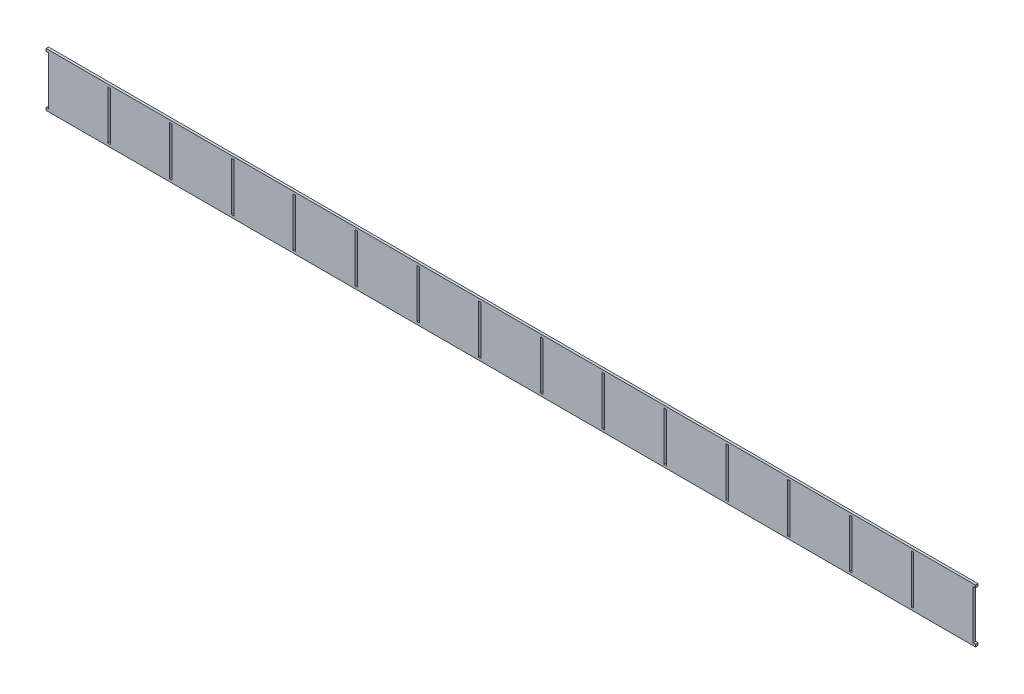
SolidWorks part; units mm, degrees
material "Cedar"
ref_plane "Front Plane" through (0, 0, 0) normal (0, 0, 1) x (1, 0, 0)
ref_plane "Top Plane" through (0, 0, 0) normal (0, 1, 0) x (1, 0, 0)
ref_plane "Right Plane" through (0, 0, 0) normal (1, 0, 0) x (0, 0, -1)
sketch "Sketch2" plane through (0, 0, 0) normal (0, 0, 1) x (1, 0, 0)
  line L0 (-778.4916, 45.21) -> (-778.4916, 41.21)
  line L1 (-778.4916, 41.21) -> (-774.4916, 41.21)
  line L2 (-774.4916, 41.21) -> (-774.4916, 1.805)
  line L3 (-774.4916, 1.805) -> (-750.4916, 1.805)
  line L4 (-756.4916, 9.805) -> (-732.4916, 9.805)
  line L5 (-750.4916, 1.805) -> (-756.4916, 9.805)
  line L6 (-738.4916, 1.805) -> (-714.4916, 1.805)
  line L7 (-738.4916, 1.805) -> (-732.4916, 9.805)
  line L8 (-578.4916, 41.21) -> (-574.4916, 41.21)
  line L9 (-714.4916, 1.805) -> (-720.4916, 9.805)
  line L10 (-720.4916, 9.805) -> (-696.4916, 9.805)
  line L11 (-702.4916, 1.805) -> (-696.4916, 9.805)
  line L12 (-702.4916, 1.805) -> (-678.4916, 1.805)
  line L13 (-778.4916, 45.21) -> (725.5084, 45.21)
  line L14 (-678.4916, 1.805) -> (-678.4916, 41.21)
  line L15 (-678.4916, 41.21) -> (-674.4916, 41.21)
  line L16 (-674.4916, 41.21) -> (-674.4916, 1.805)
  line L17 (-674.4916, 1.805) -> (-650.4916, 1.805)
  line L18 (-656.4916, 9.805) -> (-632.4916, 9.805)
  line L19 (-650.4916, 1.805) -> (-656.4916, 9.805)
  line L20 (-638.4916, 1.805) -> (-614.4916, 1.805)
  line L21 (-638.4916, 1.805) -> (-632.4916, 9.805)
  line L22 (-614.4916, 1.805) -> (-620.4916, 9.805)
  line L23 (-620.4916, 9.805) -> (-596.4916, 9.805)
  line L24 (-602.4916, 1.805) -> (-596.4916, 9.805)
  line L25 (-602.4916, 1.805) -> (-578.4916, 1.805)
  line L26 (-578.4916, 1.805) -> (-578.4916, 41.21)
  line L27 (-774.4916, 1.805) -> (855.8499, 1.805) construction
  line L28 (-574.4916, 41.21) -> (-574.4916, 1.805)
  line L29 (-574.4916, 1.805) -> (-550.4916, 1.805)
  line L30 (-556.4916, 9.805) -> (-532.4916, 9.805)
  line L31 (-550.4916, 1.805) -> (-556.4916, 9.805)
  line L32 (-538.4916, 1.805) -> (-514.4916, 1.805)
  line L33 (-538.4916, 1.805) -> (-532.4916, 9.805)
  line L34 (-514.4916, 1.805) -> (-520.4916, 9.805)
  line L35 (-520.4916, 9.805) -> (-496.4916, 9.805)
  line L36 (-502.4916, 1.805) -> (-496.4916, 9.805)
  line L37 (-502.4916, 1.805) -> (-478.4916, 1.805)
  line L38 (-478.4916, 1.805) -> (-478.4916, 41.21)
  line L39 (-478.4916, 41.21) -> (-474.4916, 41.21)
  line L40 (-474.4916, 41.21) -> (-474.4916, 1.805)
  line L41 (-474.4916, 1.805) -> (-450.4916, 1.805)
  line L42 (-456.4916, 9.805) -> (-432.4916, 9.805)
  line L43 (-450.4916, 1.805) -> (-456.4916, 9.805)
  line L44 (-438.4916, 1.805) -> (-414.4916, 1.805)
  line L45 (-438.4916, 1.805) -> (-432.4916, 9.805)
  line L46 (-414.4916, 1.805) -> (-420.4916, 9.805)
  line L47 (-420.4916, 9.805) -> (-396.4916, 9.805)
  line L48 (-402.4916, 1.805) -> (-396.4916, 9.805)
  line L49 (-402.4916, 1.805) -> (-378.4916, 1.805)
  line L50 (-378.4916, 1.805) -> (-378.4916, 41.21)
  line L51 (-378.4916, 41.21) -> (-374.4916, 41.21)
  line L52 (-374.4916, 41.21) -> (-374.4916, 1.805)
  line L53 (-374.4916, 1.805) -> (-350.4916, 1.805)
  line L54 (-356.4916, 9.805) -> (-332.4916, 9.805)
  line L55 (-350.4916, 1.805) -> (-356.4916, 9.805)
  line L56 (-338.4916, 1.805) -> (-314.4916, 1.805)
  line L57 (-338.4916, 1.805) -> (-332.4916, 9.805)
  line L58 (-314.4916, 1.805) -> (-320.4916, 9.805)
  line L59 (-320.4916, 9.805) -> (-296.4916, 9.805)
  line L60 (-302.4916, 1.805) -> (-296.4916, 9.805)
  line L61 (-302.4916, 1.805) -> (-278.4916, 1.805)
  line L62 (-278.4916, 1.805) -> (-278.4916, 41.21)
  line L63 (-278.4916, 41.21) -> (-274.4916, 41.21)
  line L64 (-274.4916, 41.21) -> (-274.4916, 1.805)
  line L65 (-274.4916, 1.805) -> (-250.4916, 1.805)
  line L66 (-256.4916, 9.805) -> (-232.4916, 9.805)
  line L67 (-250.4916, 1.805) -> (-256.4916, 9.805)
  line L68 (-238.4916, 1.805) -> (-214.4916, 1.805)
  line L69 (-238.4916, 1.805) -> (-232.4916, 9.805)
  line L70 (-214.4916, 1.805) -> (-220.4916, 9.805)
  line L71 (-220.4916, 9.805) -> (-196.4916, 9.805)
  line L72 (-202.4916, 1.805) -> (-196.4916, 9.805)
  line L73 (-202.4916, 1.805) -> (-178.4916, 1.805)
  line L74 (-178.4916, 1.805) -> (-178.4916, 41.21)
  line L75 (-178.4916, 41.21) -> (-174.4916, 41.21)
  line L76 (-174.4916, 41.21) -> (-174.4916, 1.805)
  line L77 (-174.4916, 1.805) -> (-150.4916, 1.805)
  line L78 (-156.4916, 9.805) -> (-132.4916, 9.805)
  line L79 (-150.4916, 1.805) -> (-156.4916, 9.805)
  line L80 (-138.4916, 1.805) -> (-114.4916, 1.805)
  line L81 (-138.4916, 1.805) -> (-132.4916, 9.805)
  line L82 (-114.4916, 1.805) -> (-120.4916, 9.805)
  line L83 (-120.4916, 9.805) -> (-96.4916, 9.805)
  line L84 (-102.4916, 1.805) -> (-96.4916, 9.805)
  line L85 (-102.4916, 1.805) -> (-78.4916, 1.805)
  line L86 (-78.4916, 1.805) -> (-78.4916, 41.21)
  line L87 (-78.4916, 41.21) -> (-74.4916, 41.21)
  line L88 (-74.4916, 41.21) -> (-74.4916, 1.805)
  line L89 (-74.4916, 1.805) -> (-50.4916, 1.805)
  line L90 (-56.4916, 9.805) -> (-32.4916, 9.805)
  line L91 (-50.4916, 1.805) -> (-56.4916, 9.805)
  line L92 (-38.4916, 1.805) -> (-14.4916, 1.805)
  line L93 (-38.4916, 1.805) -> (-32.4916, 9.805)
  line L94 (-14.4916, 1.805) -> (-20.4916, 9.805)
  line L95 (-20.4916, 9.805) -> (3.5084, 9.805)
  line L96 (-2.4916, 1.805) -> (3.5084, 9.805)
  line L97 (-2.4916, 1.805) -> (21.5084, 1.805)
  line L98 (21.5084, 1.805) -> (21.5084, 41.21)
  line L99 (21.5084, 41.21) -> (25.5084, 41.21)
  line L100 (25.5084, 41.21) -> (25.5084, 1.805)
  line L101 (25.5084, 1.805) -> (49.5084, 1.805)
  line L102 (43.5084, 9.805) -> (67.5084, 9.805)
  line L103 (49.5084, 1.805) -> (43.5084, 9.805)
  line L104 (61.5084, 1.805) -> (85.5084, 1.805)
  line L105 (61.5084, 1.805) -> (67.5084, 9.805)
  line L106 (85.5084, 1.805) -> (79.5084, 9.805)
  line L107 (79.5084, 9.805) -> (103.5084, 9.805)
  line L108 (97.5084, 1.805) -> (103.5084, 9.805)
  line L109 (97.5084, 1.805) -> (121.5084, 1.805)
  line L110 (121.5084, 1.805) -> (121.5084, 41.21)
  line L111 (121.5084, 41.21) -> (125.5084, 41.21)
  line L112 (125.5084, 41.21) -> (125.5084, 1.805)
  line L113 (125.5084, 1.805) -> (149.5084, 1.805)
  line L114 (143.5084, 9.805) -> (167.5084, 9.805)
  line L115 (149.5084, 1.805) -> (143.5084, 9.805)
  line L116 (161.5084, 1.805) -> (185.5084, 1.805)
  line L117 (161.5084, 1.805) -> (167.5084, 9.805)
  line L118 (185.5084, 1.805) -> (179.5084, 9.805)
  line L119 (179.5084, 9.805) -> (203.5084, 9.805)
  line L120 (197.5084, 1.805) -> (203.5084, 9.805)
  line L121 (197.5084, 1.805) -> (221.5084, 1.805)
  line L122 (221.5084, 1.805) -> (221.5084, 41.21)
  line L123 (221.5084, 41.21) -> (225.5084, 41.21)
  line L124 (225.5084, 41.21) -> (225.5084, 1.805)
  line L125 (225.5084, 1.805) -> (249.5084, 1.805)
  line L126 (243.5084, 9.805) -> (267.5084, 9.805)
  line L127 (249.5084, 1.805) -> (243.5084, 9.805)
  line L128 (261.5084, 1.805) -> (285.5084, 1.805)
  line L129 (261.5084, 1.805) -> (267.5084, 9.805)
  line L130 (285.5084, 1.805) -> (279.5084, 9.805)
  line L131 (279.5084, 9.805) -> (303.5084, 9.805)
  line L132 (297.5084, 1.805) -> (303.5084, 9.805)
  line L133 (297.5084, 1.805) -> (321.5084, 1.805)
  line L134 (321.5084, 1.805) -> (321.5084, 41.21)
  line L135 (321.5084, 41.21) -> (325.5084, 41.21)
  line L136 (325.5084, 41.21) -> (325.5084, 1.805)
  line L137 (325.5084, 1.805) -> (349.5084, 1.805)
  line L138 (343.5084, 9.805) -> (367.5084, 9.805)
  line L139 (349.5084, 1.805) -> (343.5084, 9.805)
  line L140 (361.5084, 1.805) -> (385.5084, 1.805)
  line L141 (361.5084, 1.805) -> (367.5084, 9.805)
  line L142 (385.5084, 1.805) -> (379.5084, 9.805)
  line L143 (379.5084, 9.805) -> (403.5084, 9.805)
  line L144 (397.5084, 1.805) -> (403.5084, 9.805)
  line L145 (397.5084, 1.805) -> (421.5084, 1.805)
  line L146 (421.5084, 1.805) -> (421.5084, 41.21)
  line L147 (421.5084, 41.21) -> (425.5084, 41.21)
  line L148 (425.5084, 41.21) -> (425.5084, 1.805)
  line L149 (425.5084, 1.805) -> (449.5084, 1.805)
  line L150 (443.5084, 9.805) -> (467.5084, 9.805)
  line L151 (449.5084, 1.805) -> (443.5084, 9.805)
  line L152 (461.5084, 1.805) -> (485.5084, 1.805)
  line L153 (461.5084, 1.805) -> (467.5084, 9.805)
  line L154 (485.5084, 1.805) -> (479.5084, 9.805)
  line L155 (479.5084, 9.805) -> (503.5084, 9.805)
  line L156 (497.5084, 1.805) -> (503.5084, 9.805)
  line L157 (497.5084, 1.805) -> (521.5084, 1.805)
  line L158 (521.5084, 1.805) -> (521.5084, 41.21)
  line L159 (521.5084, 41.21) -> (525.5084, 41.21)
  line L160 (525.5084, 41.21) -> (525.5084, 1.805)
  line L161 (525.5084, 1.805) -> (549.5084, 1.805)
  line L162 (543.5084, 9.805) -> (567.5084, 9.805)
  line L163 (549.5084, 1.805) -> (543.5084, 9.805)
  line L164 (561.5084, 1.805) -> (585.5084, 1.805)
  line L165 (561.5084, 1.805) -> (567.5084, 9.805)
  line L166 (585.5084, 1.805) -> (579.5084, 9.805)
  line L167 (579.5084, 9.805) -> (603.5084, 9.805)
  line L168 (597.5084, 1.805) -> (603.5084, 9.805)
  line L169 (597.5084, 1.805) -> (621.5084, 1.805)
  line L170 (621.5084, 1.805) -> (621.5084, 41.21)
  line L171 (621.5084, 41.21) -> (625.5084, 41.21)
  line L172 (625.5084, 41.21) -> (625.5084, 1.805)
  line L173 (625.5084, 1.805) -> (649.5084, 1.805)
  line L174 (643.5084, 9.805) -> (667.5084, 9.805)
  line L175 (649.5084, 1.805) -> (643.5084, 9.805)
  line L176 (661.5084, 1.805) -> (685.5084, 1.805)
  line L177 (661.5084, 1.805) -> (667.5084, 9.805)
  line L178 (685.5084, 1.805) -> (679.5084, 9.805)
  line L179 (679.5084, 9.805) -> (703.5084, 9.805)
  line L180 (697.5084, 1.805) -> (703.5084, 9.805)
  line L181 (697.5084, 1.805) -> (721.5084, 1.805)
  line L182 (721.5084, 1.805) -> (721.5084, 41.21)
  line L183 (725.5084, 45.21) -> (725.5084, 41.21)
  line L184 (725.5084, 41.21) -> (721.5084, 41.21)
  dimension "D2" = 4
  dimension "D3" = 4
  dimension "D4" = 1504
  dimension "D5" = 24
  dimension "D6" = 24
  dimension "D7" = 6
  dimension "D8" = 8
  dimension "D9" = 24
  dimension "D10" = 6
  dimension "D11" = 15
extrude "Boss-Extrude1" add sketch "Sketch2" along normal blind 4
sketch "Sketch3" plane through (0, 0, 4) normal (0, 0, 1) x (1, 0, 0)
  line L0 (-774.4916, 1.805) -> (-774.4916, -37.605)
  line L1 (-774.4916, -37.605) -> (-778.4916, -37.605)
  line L2 (-778.4916, -37.605) -> (-778.4916, -41.605)
  line L3 (-778.4916, -41.605) -> (725.5084, -41.605)
  line L4 (-674.4916, 1.805) -> (-674.4916, -37.605)
  line L5 (-774.4916, 1.805) -> (-750.4916, 1.805)
  line L6 (-750.4916, 1.805) -> (-756.4916, 9.805)
  line L7 (-756.4916, 9.805) -> (-732.4916, 9.805)
  line L8 (-732.4916, 9.805) -> (-738.4916, 1.805)
  line L9 (-738.4916, 1.805) -> (-714.4916, 1.805)
  line L10 (-714.4916, 1.805) -> (-720.4916, 9.805)
  line L11 (-720.4916, 9.805) -> (-696.4916, 9.805)
  line L12 (-696.4916, 9.805) -> (-702.4916, 1.805)
  line L13 (-702.4916, 1.805) -> (-678.4916, 1.805)
  line L14 (-678.4916, 1.805) -> (-678.4916, -37.605)
  line L15 (-674.4916, -37.605) -> (-678.4916, -37.605)
  line L16 (-674.4916, 1.805) -> (-650.4916, 1.805)
  line L17 (-650.4916, 1.805) -> (-656.4916, 9.805)
  line L18 (-656.4916, 9.805) -> (-632.4916, 9.805)
  line L19 (-632.4916, 9.805) -> (-638.4916, 1.805)
  line L20 (-638.4916, 1.805) -> (-614.4916, 1.805)
  line L21 (-614.4916, 1.805) -> (-620.4916, 9.805)
  line L22 (-620.4916, 9.805) -> (-596.4916, 9.805)
  line L23 (-596.4916, 9.805) -> (-602.4916, 1.805)
  line L24 (-602.4916, 1.805) -> (-578.4916, 1.805)
  line L25 (-578.4916, 1.805) -> (-578.4916, -37.605)
  line L26 (-574.4916, 1.805) -> (-574.4916, -37.605)
  line L27 (-574.4916, -37.605) -> (-578.4916, -37.605)
  line L28 (-574.4916, 1.805) -> (-550.4916, 1.805)
  line L29 (-550.4916, 1.805) -> (-556.4916, 9.805)
  line L30 (-556.4916, 9.805) -> (-532.4916, 9.805)
  line L31 (-532.4916, 9.805) -> (-538.4916, 1.805)
  line L32 (-538.4916, 1.805) -> (-514.4916, 1.805)
  line L33 (-514.4916, 1.805) -> (-520.4916, 9.805)
  line L34 (-520.4916, 9.805) -> (-496.4916, 9.805)
  line L35 (-496.4916, 9.805) -> (-502.4916, 1.805)
  line L36 (-502.4916, 1.805) -> (-478.4916, 1.805)
  line L37 (-478.4916, 1.805) -> (-478.4916, -37.605)
  line L38 (-474.4916, 1.805) -> (-474.4916, -37.605)
  line L39 (-474.4916, -37.605) -> (-478.4916, -37.605)
  line L40 (-474.4916, 1.805) -> (-450.4916, 1.805)
  line L41 (-450.4916, 1.805) -> (-456.4916, 9.805)
  line L42 (-456.4916, 9.805) -> (-432.4916, 9.805)
  line L43 (-432.4916, 9.805) -> (-438.4916, 1.805)
  line L44 (-438.4916, 1.805) -> (-414.4916, 1.805)
  line L45 (-414.4916, 1.805) -> (-420.4916, 9.805)
  line L46 (-420.4916, 9.805) -> (-396.4916, 9.805)
  line L47 (-396.4916, 9.805) -> (-402.4916, 1.805)
  line L48 (-402.4916, 1.805) -> (-378.4916, 1.805)
  line L49 (-378.4916, 1.805) -> (-378.4916, -37.605)
  line L50 (-374.4916, 1.805) -> (-374.4916, -37.605)
  line L51 (-374.4916, -37.605) -> (-378.4916, -37.605)
  line L52 (-374.4916, 1.805) -> (-350.4916, 1.805)
  line L53 (-350.4916, 1.805) -> (-356.4916, 9.805)
  line L54 (-356.4916, 9.805) -> (-332.4916, 9.805)
  line L55 (-332.4916, 9.805) -> (-338.4916, 1.805)
  line L56 (-338.4916, 1.805) -> (-314.4916, 1.805)
  line L57 (-314.4916, 1.805) -> (-320.4916, 9.805)
  line L58 (-320.4916, 9.805) -> (-296.4916, 9.805)
  line L59 (-296.4916, 9.805) -> (-302.4916, 1.805)
  line L60 (-302.4916, 1.805) -> (-278.4916, 1.805)
  line L61 (-278.4916, 1.805) -> (-278.4916, -37.605)
  line L62 (-274.4916, 1.805) -> (-274.4916, -37.605)
  line L63 (-274.4916, -37.605) -> (-278.4916, -37.605)
  line L64 (-274.4916, 1.805) -> (-250.4916, 1.805)
  line L65 (-250.4916, 1.805) -> (-256.4916, 9.805)
  line L66 (-256.4916, 9.805) -> (-232.4916, 9.805)
  line L67 (-232.4916, 9.805) -> (-238.4916, 1.805)
  line L68 (-238.4916, 1.805) -> (-214.4916, 1.805)
  line L69 (-214.4916, 1.805) -> (-220.4916, 9.805)
  line L70 (-220.4916, 9.805) -> (-196.4916, 9.805)
  line L71 (-196.4916, 9.805) -> (-202.4916, 1.805)
  line L72 (-202.4916, 1.805) -> (-178.4916, 1.805)
  line L73 (-178.4916, 1.805) -> (-178.4916, -37.605)
  line L74 (-174.4916, 1.805) -> (-174.4916, -37.605)
  line L75 (-174.4916, -37.605) -> (-178.4916, -37.605)
  line L76 (-174.4916, 1.805) -> (-150.4916, 1.805)
  line L77 (-150.4916, 1.805) -> (-156.4916, 9.805)
  line L78 (-156.4916, 9.805) -> (-132.4916, 9.805)
  line L79 (-132.4916, 9.805) -> (-138.4916, 1.805)
  line L80 (-138.4916, 1.805) -> (-114.4916, 1.805)
  line L81 (-114.4916, 1.805) -> (-120.4916, 9.805)
  line L82 (-120.4916, 9.805) -> (-96.4916, 9.805)
  line L83 (-96.4916, 9.805) -> (-102.4916, 1.805)
  line L84 (-102.4916, 1.805) -> (-78.4916, 1.805)
  line L85 (-78.4916, 1.805) -> (-78.4916, -37.605)
  line L86 (-74.4916, 1.805) -> (-74.4916, -37.605)
  line L87 (-74.4916, -37.605) -> (-78.4916, -37.605)
  line L88 (-74.4916, 1.805) -> (-50.4916, 1.805)
  line L89 (-50.4916, 1.805) -> (-56.4916, 9.805)
  line L90 (-56.4916, 9.805) -> (-32.4916, 9.805)
  line L91 (-32.4916, 9.805) -> (-38.4916, 1.805)
  line L92 (-38.4916, 1.805) -> (-14.4916, 1.805)
  line L93 (-14.4916, 1.805) -> (-20.4916, 9.805)
  line L94 (-20.4916, 9.805) -> (3.5084, 9.805)
  line L95 (3.5084, 9.805) -> (-2.4916, 1.805)
  line L96 (-2.4916, 1.805) -> (21.5084, 1.805)
  line L97 (21.5084, 1.805) -> (21.5084, -37.605)
  line L98 (25.5084, 1.805) -> (25.5084, -37.605)
  line L99 (25.5084, -37.605) -> (21.5084, -37.605)
  line L100 (25.5084, 1.805) -> (49.5084, 1.805)
  line L101 (49.5084, 1.805) -> (43.5084, 9.805)
  line L102 (43.5084, 9.805) -> (67.5084, 9.805)
  line L103 (67.5084, 9.805) -> (61.5084, 1.805)
  line L104 (61.5084, 1.805) -> (85.5084, 1.805)
  line L105 (85.5084, 1.805) -> (79.5084, 9.805)
  line L106 (79.5084, 9.805) -> (103.5084, 9.805)
  line L107 (103.5084, 9.805) -> (97.5084, 1.805)
  line L108 (97.5084, 1.805) -> (121.5084, 1.805)
  line L109 (121.5084, 1.805) -> (121.5084, -37.605)
  line L110 (125.5084, 1.805) -> (125.5084, -37.605)
  line L111 (125.5084, -37.605) -> (121.5084, -37.605)
  line L112 (125.5084, 1.805) -> (149.5084, 1.805)
  line L113 (149.5084, 1.805) -> (143.5084, 9.805)
  line L114 (143.5084, 9.805) -> (167.5084, 9.805)
  line L115 (167.5084, 9.805) -> (161.5084, 1.805)
  line L116 (161.5084, 1.805) -> (185.5084, 1.805)
  line L117 (185.5084, 1.805) -> (179.5084, 9.805)
  line L118 (179.5084, 9.805) -> (203.5084, 9.805)
  line L119 (203.5084, 9.805) -> (197.5084, 1.805)
  line L120 (197.5084, 1.805) -> (221.5084, 1.805)
  line L121 (221.5084, 1.805) -> (221.5084, -37.605)
  line L122 (225.5084, 1.805) -> (225.5084, -37.605)
  line L123 (225.5084, -37.605) -> (221.5084, -37.605)
  line L124 (225.5084, 1.805) -> (249.5084, 1.805)
  line L125 (249.5084, 1.805) -> (243.5084, 9.805)
  line L126 (243.5084, 9.805) -> (267.5084, 9.805)
  line L127 (267.5084, 9.805) -> (261.5084, 1.805)
  line L128 (261.5084, 1.805) -> (285.5084, 1.805)
  line L129 (285.5084, 1.805) -> (279.5084, 9.805)
  line L130 (279.5084, 9.805) -> (303.5084, 9.805)
  line L131 (303.5084, 9.805) -> (297.5084, 1.805)
  line L132 (297.5084, 1.805) -> (321.5084, 1.805)
  line L133 (321.5084, 1.805) -> (321.5084, -37.605)
  line L134 (325.5084, 1.805) -> (325.5084, -37.605)
  line L135 (325.5084, -37.605) -> (321.5084, -37.605)
  line L136 (325.5084, 1.805) -> (349.5084, 1.805)
  line L137 (349.5084, 1.805) -> (343.5084, 9.805)
  line L138 (343.5084, 9.805) -> (367.5084, 9.805)
  line L139 (367.5084, 9.805) -> (361.5084, 1.805)
  line L140 (361.5084, 1.805) -> (385.5084, 1.805)
  line L141 (385.5084, 1.805) -> (379.5084, 9.805)
  line L142 (379.5084, 9.805) -> (403.5084, 9.805)
  line L143 (403.5084, 9.805) -> (397.5084, 1.805)
  line L144 (397.5084, 1.805) -> (421.5084, 1.805)
  line L145 (421.5084, 1.805) -> (421.5084, -37.605)
  line L146 (425.5084, 1.805) -> (425.5084, -37.605)
  line L147 (425.5084, -37.605) -> (421.5084, -37.605)
  line L148 (425.5084, 1.805) -> (449.5084, 1.805)
  line L149 (449.5084, 1.805) -> (443.5084, 9.805)
  line L150 (443.5084, 9.805) -> (467.5084, 9.805)
  line L151 (467.5084, 9.805) -> (461.5084, 1.805)
  line L152 (461.5084, 1.805) -> (485.5084, 1.805)
  line L153 (485.5084, 1.805) -> (479.5084, 9.805)
  line L154 (479.5084, 9.805) -> (503.5084, 9.805)
  line L155 (503.5084, 9.805) -> (497.5084, 1.805)
  line L156 (497.5084, 1.805) -> (521.5084, 1.805)
  line L157 (521.5084, 1.805) -> (521.5084, -37.605)
  line L158 (525.5084, 1.805) -> (525.5084, -37.605)
  line L159 (525.5084, -37.605) -> (521.5084, -37.605)
  line L160 (525.5084, 1.805) -> (549.5084, 1.805)
  line L161 (549.5084, 1.805) -> (543.5084, 9.805)
  line L162 (543.5084, 9.805) -> (567.5084, 9.805)
  line L163 (567.5084, 9.805) -> (561.5084, 1.805)
  line L164 (561.5084, 1.805) -> (585.5084, 1.805)
  line L165 (585.5084, 1.805) -> (579.5084, 9.805)
  line L166 (579.5084, 9.805) -> (603.5084, 9.805)
  line L167 (603.5084, 9.805) -> (597.5084, 1.805)
  line L168 (597.5084, 1.805) -> (621.5084, 1.805)
  line L169 (621.5084, 1.805) -> (621.5084, -37.605)
  line L170 (625.5084, 1.805) -> (625.5084, -37.605)
  line L171 (625.5084, -37.605) -> (621.5084, -37.605)
  line L172 (625.5084, 1.805) -> (649.5084, 1.805)
  line L173 (649.5084, 1.805) -> (643.5084, 9.805)
  line L174 (643.5084, 9.805) -> (667.5084, 9.805)
  line L175 (667.5084, 9.805) -> (661.5084, 1.805)
  line L176 (661.5084, 1.805) -> (685.5084, 1.805)
  line L177 (685.5084, 1.805) -> (679.5084, 9.805)
  line L178 (679.5084, 9.805) -> (703.5084, 9.805)
  line L179 (703.5084, 9.805) -> (697.5084, 1.805)
  line L180 (697.5084, 1.805) -> (721.5084, 1.805)
  line L181 (721.5084, 1.805) -> (721.5084, -37.605)
  line L182 (721.5084, -37.605) -> (725.5084, -37.605)
  line L183 (725.5084, -37.605) -> (725.5084, -41.605)
  dimension "D1" = 1504
  dimension "D2" = 4
  dimension "D3" = 39.41
  dimension "D4" = 4
  dimension "D5" = 15
extrude "Boss-Extrude2" add sketch "Sketch3" against normal blind 4
